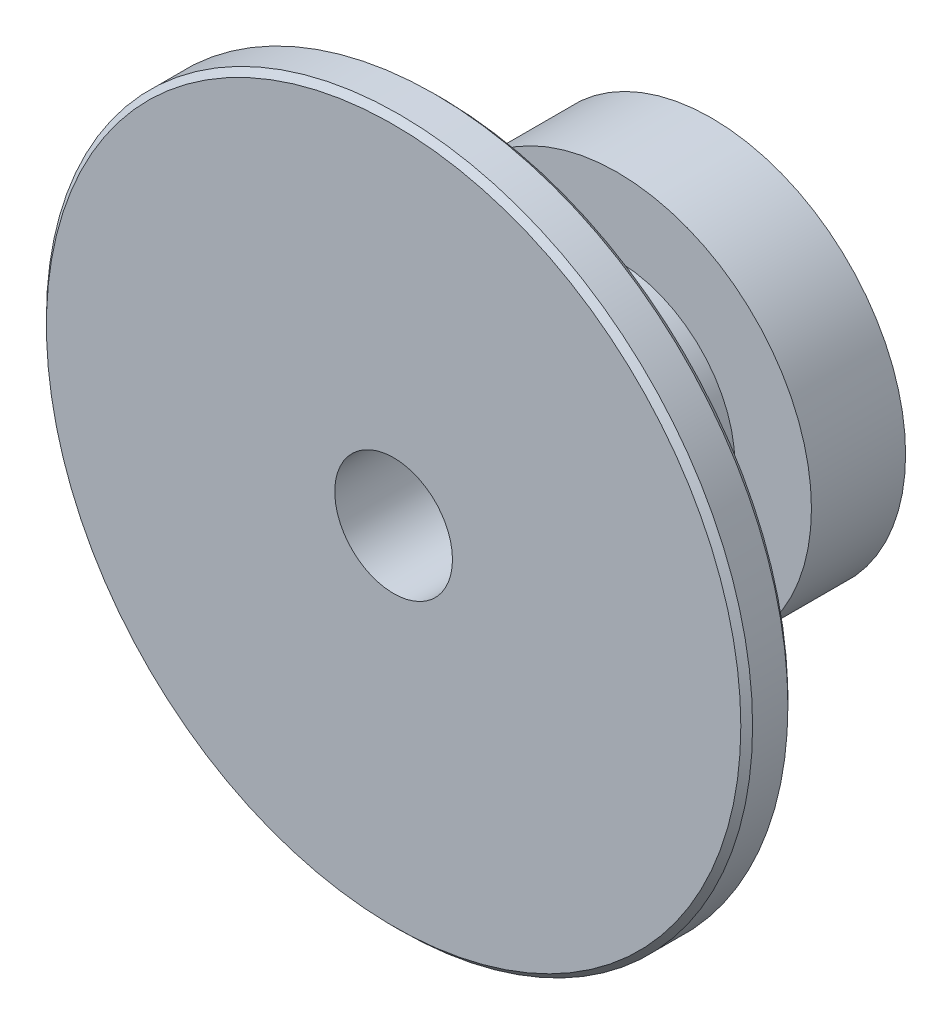
SolidWorks part; units mm, degrees
material "AISI 1020"
ref_plane "Front Plane" through (0, 0, 0) normal (0, 0, 1) x (1, 0, 0)
ref_plane "Top Plane" through (0, 0, 0) normal (0, 1, 0) x (1, 0, 0)
ref_plane "Right Plane" through (0, 0, 0) normal (1, 0, 0) x (0, 0, -1)
sketch "Sketch1" plane through (0, 0, 0) normal (0, 1, 0) x (1, 0, 0)
  line L0 (0, -17.8725) -> (0, 33.6003) construction
  line L1 (6, 0) -> (0, 0)
  line L2 (15, 0) -> (6, 0)
  line L3 (15, 0) -> (15, 2)
  line L4 (15, 2) -> (8.25, 2)
  line L5 (0, 0) -> (0, 6.5)
  line L8 (0, 6.5) -> (8.25, 6.5)
  line L9 (8.25, 2) -> (8.25, 6.5)
  dimension "D1" = 15
  dimension "D2" = 2
  dimension "D3" = 8.25
  dimension "D4" = 4.5
revolve "Revolve1" add sketch "Sketch1" angle 360 about L0
chamfer "Chamfer1" distance 0.25 angle 45 2 edges at (15, 0, 0) (15, 0, -2)
sketch "Sketch2" plane through (0, 0, -6.5) normal (0, 0, -1) x (-1, 0, 0)
  circle A0 centre (0, 0) radius 2.5
  dimension "D1" = 5
extrude "Cut-Extrude1" cut sketch "Sketch2" against normal blind 10
sketch "Sketch5" plane through (0, 0, 0) normal (0, 1, 0) x (1, 0, 0)
  line L0 (2.5, 3.2376) -> (2.5, 13.5)
  line L1 (5, 9.5) -> (5, 3.2376)
  line L2 (5, 3.2376) -> (2.5, 3.2376)
  line L3 (2.5, 13.5) -> (8.25, 13.5)
  line L4 (0, 0) -> (0, 19.4667) construction
  line L5 (8.25, 13.5) -> (8.25, 9.5)
  line L6 (8.25, 9.5) -> (5, 9.5)
  line L7 (8.25, 6.5) -> (-8.25, 6.5) construction
  dimension "D1" = 5
  dimension "D2" = 10
  dimension "D3" = 16.5
  dimension "D4" = 3
  dimension "D5" = 4
revolve "Revolve2" add sketch "Sketch5" angle 360 about L4
